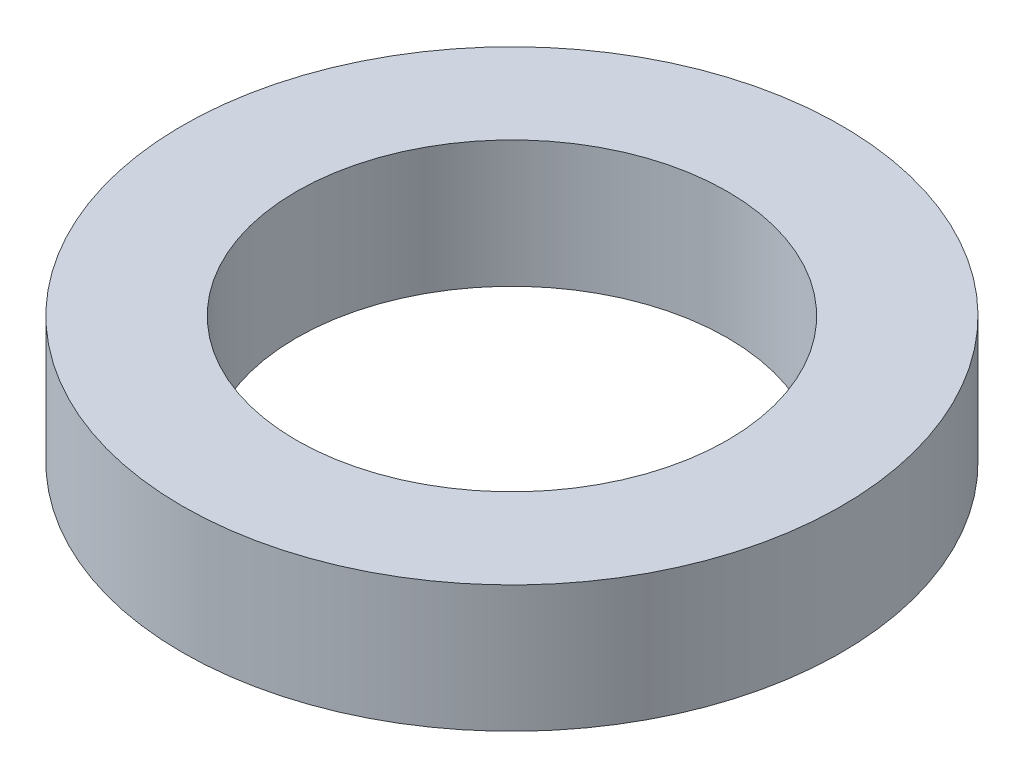
SolidWorks part; units mm, degrees
ref_plane "Front Plane" through (0, 0, 0) normal (0, 0, 1) x (1, 0, 0)
ref_plane "Top Plane" through (0, 0, 0) normal (0, 1, 0) x (1, 0, 0)
ref_plane "Right Plane" through (0, 0, 0) normal (1, 0, 0) x (0, 0, -1)
sketch "Sketch1" plane through (0, 0, 0) normal (0, 1, 0) x (1, 0, 0)
  circle A0 centre (0, 0) radius 13
  circle A1 centre (0, 0) radius 8.5
  dimension "D1" = 26
  dimension "D2" = 17
extrude "Boss-Extrude1" add sketch "Sketch1" along normal blind 5
